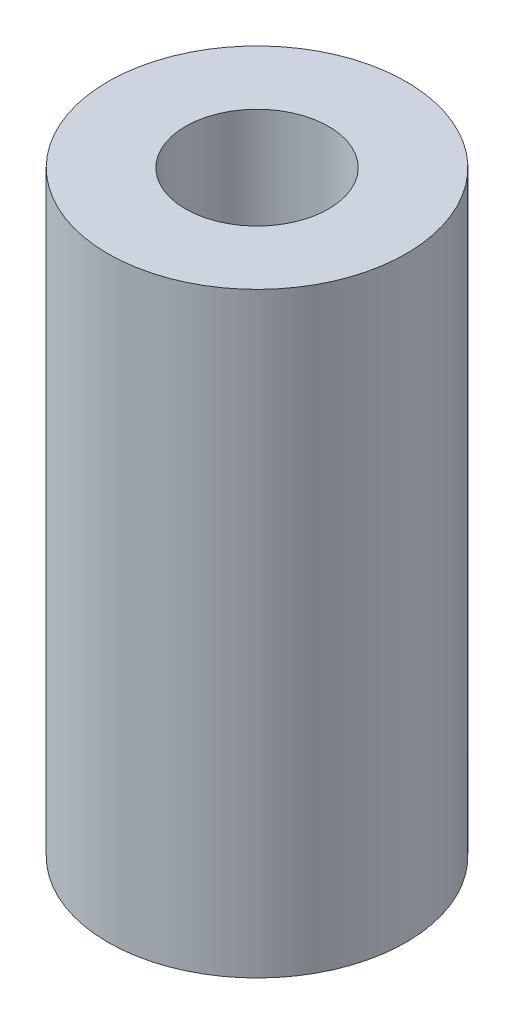
SolidWorks part; units mm, degrees
ref_plane "Ebene vorne" through (0, 0, 0) normal (0, 0, 1) x (1, 0, 0)
ref_plane "Ebene oben" through (0, 0, 0) normal (0, 1, 0) x (1, 0, 0)
ref_plane "Ebene rechts" through (0, 0, 0) normal (1, 0, 0) x (0, 0, -1)
sketch "Skizze1" plane through (0, 0, 0) normal (0, 1, 0) x (1, 0, 0)
  circle A0 centre (0, 0) radius 2.5
extrude "Aufsatz-Linear austragen1" add sketch "Skizze1" along normal blind 10
sketch "Skizze2" plane through (0, 10, 0) normal (0, 1, 0) x (1, 0, 0)
  circle A0 centre (0, 0) radius 1.2
extrude "Schnitt-Linear austragen1" cut sketch "Skizze2" against normal blind 3
sketch "Skizze3" plane through (0, 0, 0) normal (0, -1, 0) x (1, 0, 0)
  circle A0 centre (0, 0) radius 1.2
extrude "Schnitt-Linear austragen2" cut sketch "Skizze3" against normal blind 3
